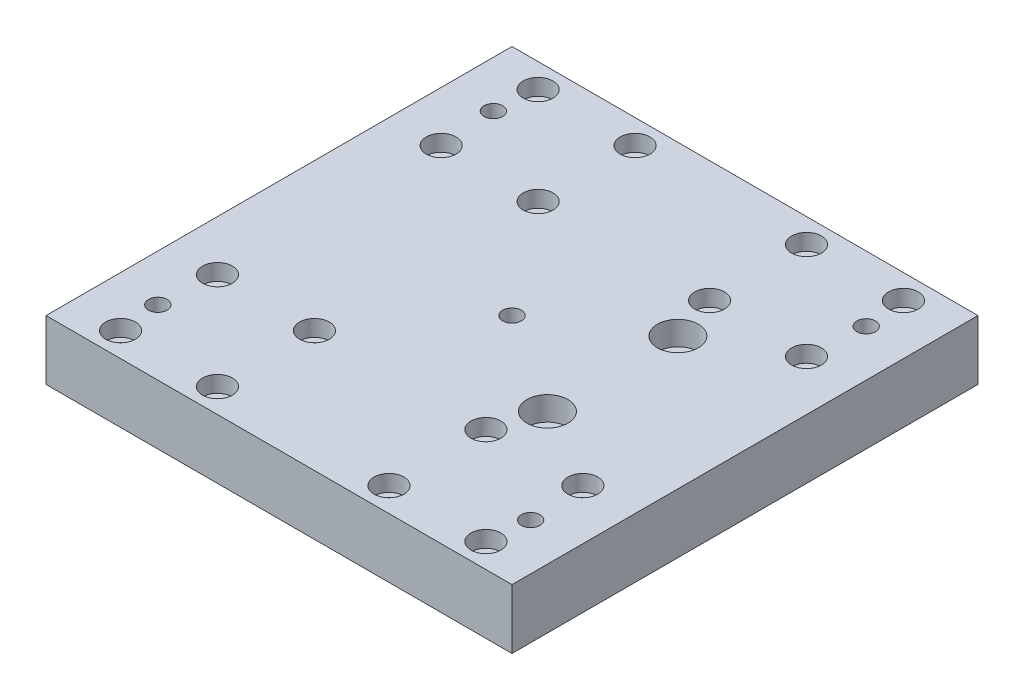
SolidWorks part; units mm, degrees
material "1023 Листовая углеродистая сталь (SS)"
ref_plane "Front" through (0, 0, 0) normal (0, 0, 1) x (1, 0, 0)
ref_plane "Top" through (0, 0, 0) normal (0, 1, 0) x (1, 0, 0)
ref_plane "Right" through (0, 0, 0) normal (1, 0, 0) x (0, 0, -1)
sketch "Sketch1" plane through (0, 0, 0) normal (0, 1, 0) x (1, 0, 0)
  line L1 (-62.5, 62.5) -> (62.5, 62.5)
  line L2 (-62.5, 62.5) -> (-62.5, -62.5)
  line L3 (-62.5, -62.5) -> (62.5, -62.5)
  line L4 (62.5, 62.5) -> (62.5, -62.5)
  line L5 (-62.5, 62.5) -> (62.5, -62.5) construction
  line L6 (-62.5, -62.5) -> (62.5, 62.5) construction
  point P0 (0, 0)
  dimension "D1" = 125
  dimension "D2" = 125
extrude "Extrude1" add sketch "Sketch1" along normal blind 16
hole_wizard "CBORE for M4 Hex Socket Head Cap Screw1" positions "Sketch2" profile "Sketch3" counterbore size "M4" standard "DIN" end condition through all
sketch "Sketch2" plane through (0, 16, 0) normal (0, 1, 0) x (1, 0, 0)
  line L1 (-49, 56) -> (-23, 56)
  line L2 (-49, 56) -> (-49, 30)
  line L3 (-49, 30) -> (-23, 30)
  line L4 (-23, 56) -> (-23, 30)
  line L5 (0, -22.0102) -> (0, 22.0102) construction
  line L7 (23, 56) -> (23, 30)
  line L8 (49, 30) -> (23, 30)
  line L9 (49, 56) -> (49, 30)
  line L10 (49, 56) -> (23, 56)
  line L11 (0, 0) -> (23, 0) construction
  line L14 (49, -56) -> (23, -56)
  line L15 (49, -56) -> (49, -30)
  line L16 (49, -30) -> (23, -30)
  line L17 (23, -56) -> (23, -30)
  line L18 (-23, -56) -> (-23, -30)
  line L19 (-49, -30) -> (-23, -30)
  line L20 (-49, -56) -> (-49, -30)
  line L21 (-49, -56) -> (-23, -56)
  point P0 (-49, 56)
  point P2 (-23, 56)
  point P4 (-49, 30)
  point P6 (-23, 30)
  point P37 (23, 30)
  point P38 (49, 30)
  point P39 (23, 56)
  point P40 (49, 56)
  point P50 (49, -56)
  point P51 (23, -56)
  point P52 (49, -30)
  point P53 (23, -30)
  point P54 (-23, -56)
  point P55 (-23, -30)
  point P56 (-49, -30)
  point P57 (-49, -56)
  dimension "D1" = 26
  dimension "D2" = 23
  dimension "D3" = 30
sketch "Sketch3" plane through (-49, 16, -56) normal (1, 0, 0) x (0, 0, 1)
  line L0 (0, 0) -> (0, 16)
  line L1 (0, 16) -> (2.25, 16)
  line L3 (2.25, 16) -> (2.25, 4.4)
  line L4 (2.25, 4.4) -> (4, 4.4)
  line L5 (4, 4.4) -> (4, 0)
  line L7 (4, 0) -> (0, 0)
  line L11 (0, -6.35) -> (0, 107.95) construction
  dimension "Диаметр сквозного отверстия" = 4.5
  dimension "Глубина сквозного отверстия" = 16
  dimension "Диаметр цековки" = 8
  dimension "Глубина цековки" = 4.4
hole_wizard "CBORE for M6 Hex Socket Head Cap Screw1" positions "Sketch4" profile "Sketch5" counterbore size "M6" standard "DIN" end condition through all
sketch "Sketch4" plane through (0, 16, 0) normal (0, 1, 0) x (1, 0, 0)
  line L0 (62.5, -62.5) -> (62.5, 62.5) construction
  line L1 (27, 17.5) -> (27, -17.5)
  line L3 (0, 0) -> (27, 0)
  point P0 (27, 17.5)
  point P2 (27, -17.5)
  dimension "D1" = 35.5
  dimension "D2" = 35
sketch "Sketch5" plane through (27, 16, -17.5) normal (1, 0, 0) x (0, 0, 1)
  line L0 (0, 0) -> (0, 16)
  line L1 (0, 16) -> (3.3, 16)
  line L3 (3.3, 16) -> (3.3, 6.4)
  line L4 (3.3, 6.4) -> (5.5, 6.4)
  line L5 (5.5, 6.4) -> (5.5, 0)
  line L7 (5.5, 0) -> (0, 0)
  line L11 (0, -6.35) -> (0, 107.95) construction
  dimension "Диаметр сквозного отверстия" = 6.6
  dimension "Глубина сквозного отверстия" = 16
  dimension "Диаметр цековки" = 11
  dimension "Глубина цековки" = 6.4
hole_wizard "M6 Tapped Hole1" positions "Sketch6" profile "Sketch7" tap size "M6" standard "DIN" end condition through all
sketch "Sketch6" plane through (0, 16, 0) normal (0, 1, 0) x (1, 0, 0)
  line L1 (50, -45) -> (-50, -45)
  line L2 (50, -45) -> (50, 45)
  line L3 (50, 45) -> (-50, 45)
  line L4 (-50, -45) -> (-50, 45)
  line L5 (50, -45) -> (-50, 45) construction
  line L6 (50, 45) -> (-50, -45) construction
  point P0 (-50, 45)
  point P3 (50, 45)
  point P6 (50, -45)
  point P9 (-50, -45)
  point P19 (0, 0)
  point P56 (0, 0)
  point P57 (50, -45)
  point P58 (50, 45)
  dimension "D1" = 90
  dimension "D2" = 100
sketch "Sketch7" plane through (-50, 16, -45) normal (1, 0, 0) x (0, 0, 1)
  line L0 (0, 0) -> (0, 16)
  line L1 (0, 16) -> (2.5, 16)
  line L2 (2.5, 16) -> (2.5, 0)
  line L5 (2.5, 0) -> (0, 0)
  line L11 (0, -6.35) -> (0, 107.95) construction
  dimension "Диаметр проходного сверла" = 5
  dimension "Глубина проходного сверла" = 16
cosmetic thread "Cosmetic Thread1" parameters "D2"=6
cosmetic thread "Cosmetic Thread2" parameters "D2"=6
cosmetic thread "Cosmetic Thread3" parameters "D2"=6
cosmetic thread "Cosmetic Thread4" parameters "D2"=6
cosmetic thread "Cosmetic Thread5" parameters "D2"=6
hole_wizard "M4 Tapped Hole1" positions "Sketch8" profile "Sketch10" tap size "M4" standard "DIN"
sketch "Sketch8" plane through (0, 0, -62.5) normal (0, 0, -1) x (-1, 0, 0)
  point P0 (36, 7.5)
  point P3 (24, 7.5)
sketch "Sketch10" plane through (-36, 7.5, -62.5) normal (1, 0, 0) x (0, 1, 0)
  line L0 (0, 0) -> (0, 12.4914)
  line L1 (0, 12.4914) -> (1.65, 11.5)
  line L2 (1.65, 11.5) -> (1.65, 0)
  line L5 (1.65, 0) -> (0, 0)
  line L10 (0, 12.4914) -> (-1.65, 11.5) construction
  line L11 (0, -6.35) -> (0, 107.95) construction
  dimension "Диаметр сверла" = 3.3
  dimension "Глубина сверла" = 11.5
  dimension "Угол заточки сверла" = 118
cosmetic thread "Cosmetic Thread6" parameters "D1"=8, "D2"=4
cosmetic thread "Cosmetic Thread7" parameters "D1"=8, "D2"=4
